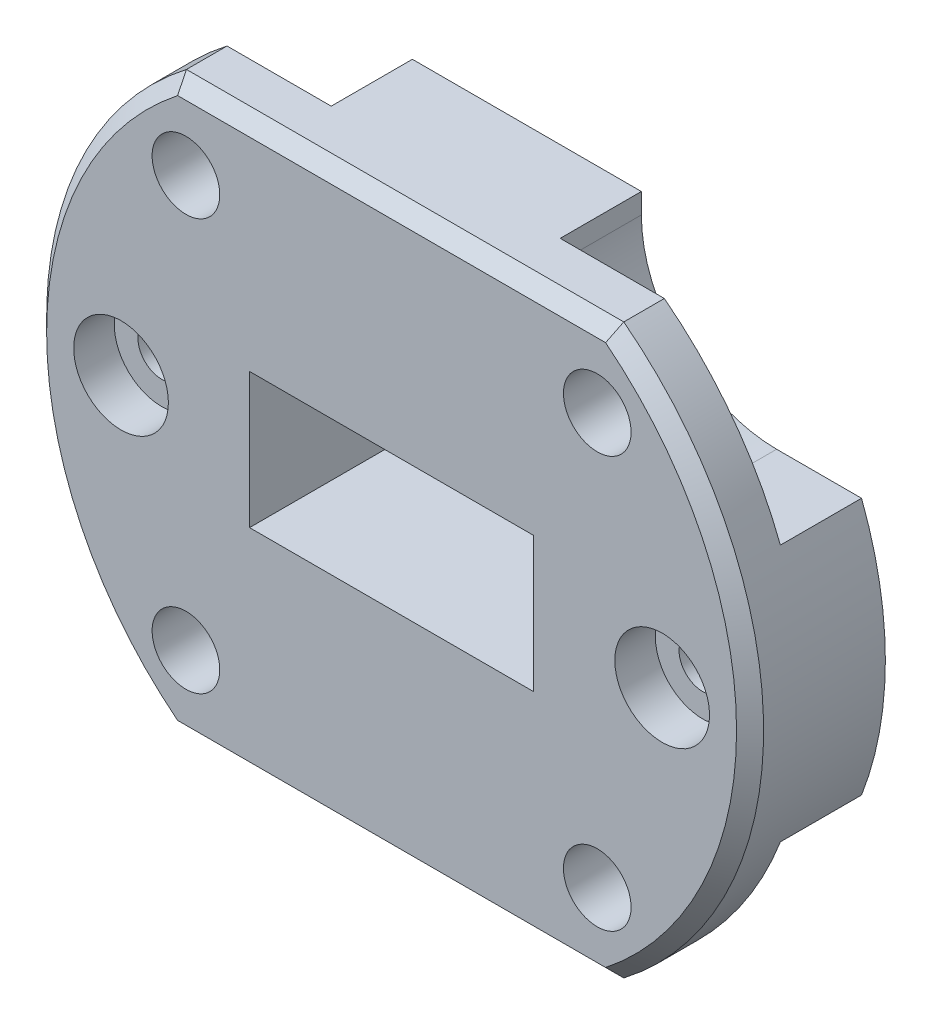
SolidWorks part; units mm, degrees
material "Латунь"
ref_plane "Спереди" through (0, 0, 0) normal (0, 0, 1) x (1, 0, 0)
ref_plane "Сверху" through (0, 0, 0) normal (0, 1, 0) x (1, 0, 0)
ref_plane "Справа" through (0, 0, 0) normal (1, 0, 0) x (0, 0, -1)
sketch "Эскиз1" plane through (0, 0, 0) normal (0, 0, 1) x (1, 0, 0)
  circle A0 centre (0, 0) radius 26.5
  dimension "D1" = 53
extrude "Бобышка-Вытянуть1" add sketch "Эскиз1" along normal blind 10
sketch "Эскиз5" plane through (0, 0, 10) normal (0, 0, 1) x (1, 0, 0)
  line L0 (-15.2028, 15.2028) -> (0, 0) construction
  line L1 (0, 0) -> (-21.5, 0) construction
  circle A0 centre (0, 0) radius 21.5 construction
  circle A1 centre (-15.2028, 15.2028) radius 2.5
  dimension "D1" = 43
  dimension "D2" = 5
  dimension "D3" = 45
extrude "Вырез-Вытянуть4" cut sketch "Эскиз5" against normal through all
pattern_circular "Круговой массив1" count 4 over 360 about axis through (0, 0, 0) along (0, 0, 1) of "Вырез-Вытянуть4"
chamfer "Фаска1" distance 1 angle 45 1 edges at (26.5, 0, 10)
sketch "Эскиз6" plane through (0, 0, 0) normal (0, 0, 1) x (1, 0, 0)
  line L0 (0, 0) -> (0, 32.6635) construction
  line L2 (0, 21) -> (30, 21)
  line L3 (0, 21) -> (0, 51)
  line L4 (0, 51) -> (30, 51)
  line L5 (30, 21) -> (30, 51)
  dimension "D1" = 21
  dimension "D2" = 30
revolve "Вырез-Повернуть1" cut sketch "Эскиз6" angle 360 about L0
mirror "Зеркальное отражение1" about plane through (0, 0, 0) normal (0, 1, 0) of "Вырез-Повернуть1"
sketch "Эскиз7" plane through (0, 0, 10) normal (0, 0, 1) x (1, 0, 0)
  point P0 (-20, 0)
  dimension "D1" = 20
sketch "Эскиз8" plane through (0, 0, 10) normal (0, 0, 1) x (1, 0, 0)
  line L1 (-10.5, -5) -> (10.5, -5)
  line L2 (-10.5, -5) -> (-10.5, 5)
  line L3 (-10.5, 5) -> (10.5, 5)
  line L4 (10.5, -5) -> (10.5, 5)
  line L5 (-10.5, -5) -> (10.5, 5) construction
  line L6 (-10.5, 5) -> (10.5, -5) construction
  point P0 (0, 0)
  dimension "D1" = 10
  dimension "D2" = 21
extrude "Вырез-Вытянуть5" cut sketch "Эскиз8" against normal through all
sketch "Эскиз9" plane through (0, 0, 0) normal (0, 0, -1) x (-1, 0, 0)
  line L0 (-16.1632, -21) -> (16.1632, -21) construction
  line L2 (18.4632, -9.5) -> (28.4632, -9.5)
  line L3 (28.4632, -9.5) -> (28.4632, -19.5)
  line L4 (28.4632, -19.5) -> (28.4632, -29.5)
  line L5 (28.4632, -29.5) -> (18.4632, -29.5)
  line L6 (8.4632, -19.5) -> (8.4632, -29.5)
  line L7 (8.4632, -29.5) -> (18.4632, -29.5)
  arc A0 (18.4632, -9.5) -> (8.4632, -19.5) centre (18.4632, -19.5) ccw
  point P4 (18.4632, -9.5)
  circle M6 centre (15.2028, -15.2028) radius 2.5
  line M11 (-16.1632, -21) -> (16.1632, -21)
  arc M12 (16.1632, -21) -> (16.1632, 21) centre (0, 0) ccw
  dimension "D1" = 20
  dimension "D2" = 1.5
  dimension "D3" = 2.3
extrude "Вырез-Вытянуть7" cut sketch "Эскиз9" against normal offset from surface (6 mm away) 4 contours L6 L7 L5 L4 L3 L2 M12 M11 | L2 A0 L6 M11 M12 M6 up to face at (0, 0, 10)
mirror "Зеркальное отражение2" about plane through (0, 0, 0) normal (0, 1, 0) of "Вырез-Вытянуть7"
mirror "Зеркальное отражение3" about plane through (0, 0, 0) normal (1, 0, 0) of "Зеркальное отражение2", "Вырез-Вытянуть7"
sketch "Эскиз12" plane through (0, 0, 10) normal (0, 0, 1) x (1, 0, 0)
  circle A0 centre (-20, 0) radius 3.5
  dimension "D2" = 7
  dimension "D1" = 20
extrude "Вырез-Вытянуть8" cut sketch "Эскиз12" against normal blind 3
sketch "Эскиз13" plane through (0, 0, 7) normal (0, 0, 1) x (1, 0, 0)
  circle A0 centre (-20, 0) radius 1.75
  dimension "D1" = 3.5
extrude "Вырез-Вытянуть9" cut sketch "Эскиз13" against normal through all
mirror "Зеркальное отражение4" about plane through (0, 0, 0) normal (1, 0, 0) of "Вырез-Вытянуть9", "Вырез-Вытянуть8"
chamfer "Фаска2" distance 1 angle 45 2 edges at (0, -21, 10) (0, 21, 10)
